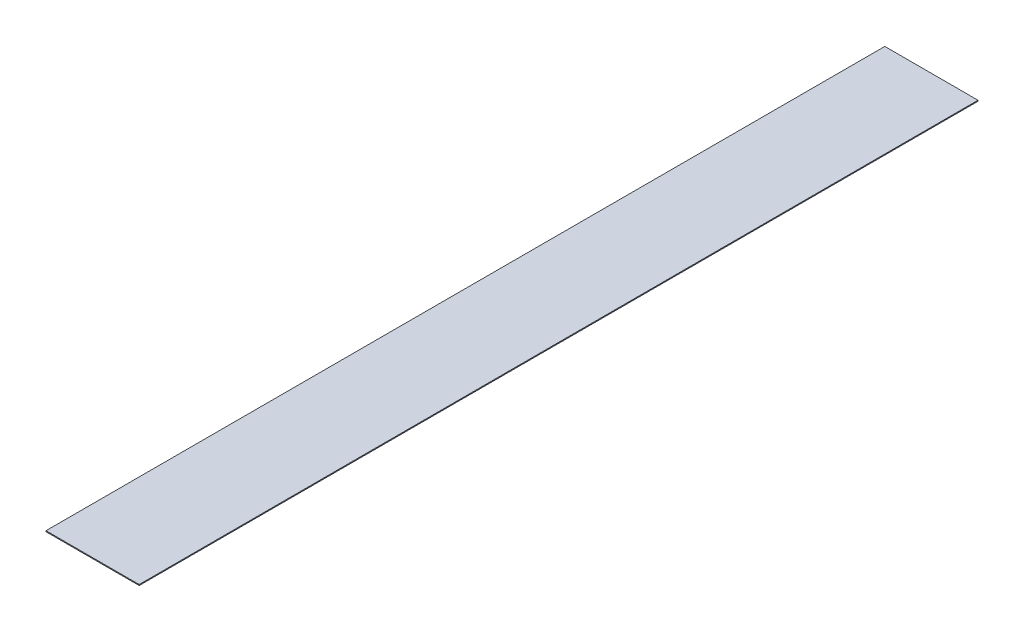
SolidWorks part; units mm, degrees
ref_plane "Front Plane" through (0, 0, 0) normal (0, 0, 1) x (1, 0, 0)
ref_plane "Top Plane" through (0, 0, 0) normal (0, 1, 0) x (1, 0, 0)
ref_plane "Right Plane" through (0, 0, 0) normal (1, 0, 0) x (0, 0, -1)
sketch "Sketch1" plane through (0, 0, 0) normal (0, 1, 0) x (1, 0, 0)
  line L1 (-25.4, 0) -> (25.4, 0)
  line L2 (-25.4, 0) -> (-25.4, 457.2)
  line L3 (-25.4, 457.2) -> (25.4, 457.2)
  line L4 (25.4, 0) -> (25.4, 457.2)
  point P4 (-23.3809, 0)
  dimension "D1" = 50.8
  dimension "D2" = 457.2
extrude "Boss-Extrude1" add sketch "Sketch1" along normal blind 0.508
